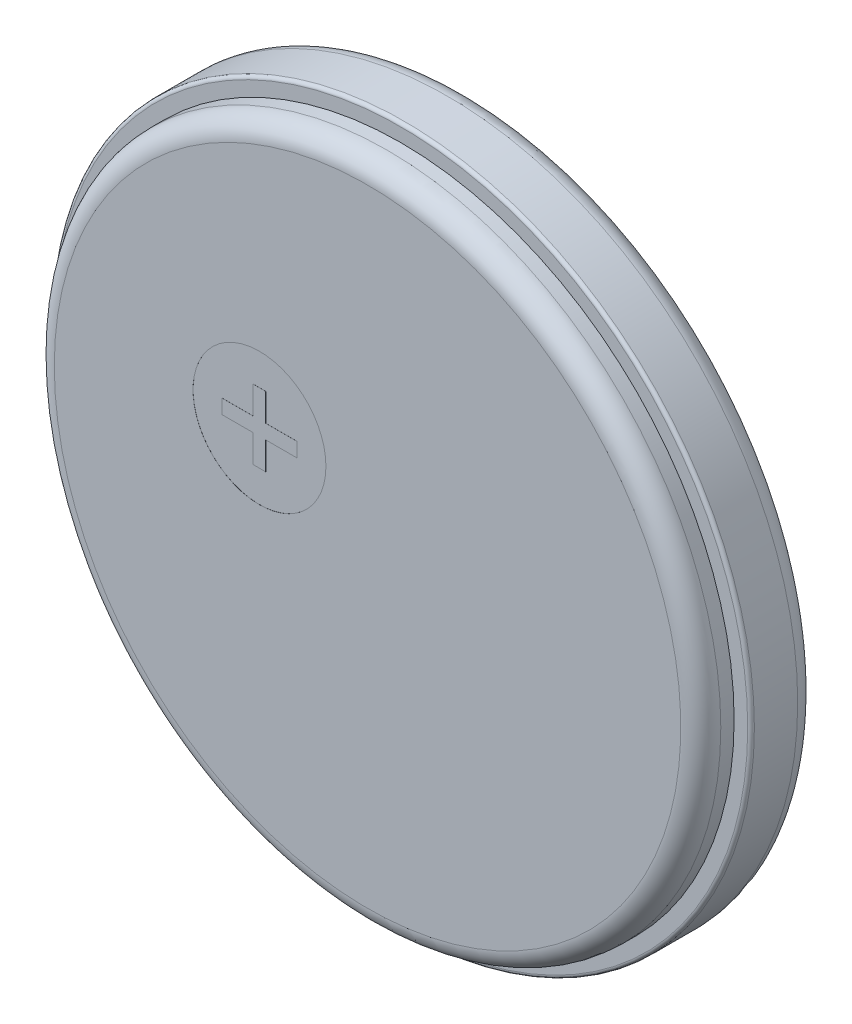
SolidWorks part; units mm, degrees
ref_plane "Front Plane" through (0, 0, 0) normal (0, 0, 1) x (1, 0, 0)
ref_plane "Top Plane" through (0, 0, 0) normal (0, 1, 0) x (1, 0, 0)
ref_plane "Right Plane" through (0, 0, 0) normal (1, 0, 0) x (0, 0, -1)
sketch "Sketch2" plane through (0, 0, 10.668) normal (0, 0, -1) x (-1, 0, 0)
  circle A0 centre (0, 31.75) radius 5
  dimension "D1" = 10
extrude "Boss-Extrude1" add sketch "Sketch2" along normal blind 0.5
fillet "Fillet1" radius 0.3 1 edges at (-5, 31.75, 10.668)
sketch "Sketch3" plane through (0, 0, 10.168) normal (0, 0, -1) x (-1, 0, 0)
  circle A2 centre (0, 31.75) radius 5.254
  circle A3 centre (0, 31.75) radius 5.254
  dimension "D1" = 0.254
extrude "Boss-Extrude2" add sketch "Sketch3" along normal blind 1
fillet "Fillet2" radius 0.3 1 edges at (-5.254, 31.75, 9.168)
fillet "Fillet3" radius 0.05 1 edges at (-5.254, 31.75, 10.168)
sketch "Sketch4" plane through (0, 0, 9.168) normal (0, 0, -1) x (-1, 0, 0)
  line L0 (-2.6501, 29.9289) -> (3.0044, 29.9289) construction
  line L1 (1.1417, 31.9299) -> (0.581, 33.5569)
  line L2 (0.581, 33.5569) -> (0.7228, 33.6419)
  line L3 (0.7228, 33.6419) -> (1.6489, 32.1001)
  line L4 (0.8246, 33.712) -> (1.7515, 32.1672)
  line L5 (0.8246, 33.712) -> (0.9402, 33.7813)
  line L6 (0.9402, 33.7813) -> (2.1566, 32.6492)
  arc A0 (1.6489, 32.1001) -> (1.7515, 32.1672) centre (0.992, 33.2168) ccw
  circle A1 centre (0.581, 33.947) radius 0.2042
  arc A3 (2.1566, 32.6492) -> (1.1417, 31.9299) centre (0.992, 33.2168) ccw
  text T0 "Lithium Ion" font "Impact" height in points 3
extrude "Cut-Extrude1" cut sketch "Sketch4" against normal blind 0.001
sketch "Sketch5" plane through (0, 0, 9.168) normal (0, 0, -1) x (-1, 0, 0)
  text T0 "Veltel" font "BankGothic Md BT" height in points 2
extrude "Cut-Extrude2" cut sketch "Sketch5" against normal blind 0.001
sketch "Sketch6" plane through (0, 0, 9.168) normal (0, 0, -1) x (-1, 0, 0)
  text T0 "CR5505" font "Century Gothic" height in points 2
extrude "Cut-Extrude3" cut sketch "Sketch6" against normal blind 0.001
sketch "Sketch7" plane through (0, 0, 9.168) normal (0, 0, -1) x (-1, 0, 0)
  line L1 (-1.3038, 33.2168) -> (-2.5226, 33.2168)
  line L2 (-1.3038, 33.2168) -> (-1.3038, 33.4152)
  line L3 (-1.3038, 33.4152) -> (-2.5226, 33.4152)
  line L4 (-2.5226, 33.2168) -> (-2.5226, 33.4152)
  line L5 (-1.3038, 33.2168) -> (-2.5226, 33.4152) construction
  line L6 (-1.3038, 33.4152) -> (-2.5226, 33.2168) construction
  circle A0 centre (-1.9132, 33.316) radius 0.8691
  point P0 (-1.9132, 33.316)
extrude "Cut-Extrude4" cut sketch "Sketch7" against normal blind 0.001
sketch "Sketch8" plane through (0, 0, 10.668) normal (0, 0, 1) x (1, 0, 0)
  line L0 (-1.7148, 32.5891) -> (-2.1834, 32.5891)
  line L1 (-1.7148, 31.9585) -> (-1.5276, 31.9585)
  line L2 (-1.7148, 32.5891) -> (-1.7148, 33.0042)
  line L3 (-1.7148, 33.0042) -> (-1.5276, 33.0042)
  line L4 (-1.5276, 31.9585) -> (-1.5276, 32.3736)
  line L5 (-1.7148, 31.9585) -> (-1.5276, 33.0042) construction
  line L6 (-1.7148, 33.0042) -> (-1.5276, 31.9585) construction
  line L7 (-1.059, 32.3736) -> (-1.5276, 32.3736)
  line L8 (-1.059, 32.3736) -> (-1.059, 32.5891)
  line L9 (-1.059, 32.5891) -> (-1.5276, 32.5891)
  line L10 (-2.1834, 32.3736) -> (-2.1834, 32.5891)
  line L11 (-1.059, 32.3736) -> (-2.1834, 32.5891) construction
  line L12 (-1.059, 32.5891) -> (-2.1834, 32.3736) construction
  line L13 (-1.7148, 31.9585) -> (-1.7148, 32.3736)
  line L14 (-1.5276, 32.5891) -> (-1.5276, 33.0042)
  line L16 (-1.7148, 32.3736) -> (-2.1834, 32.3736)
  circle A0 centre (-1.6212, 32.4814) radius 0.9969
  point P0 (-1.6212, 32.4814)
  point P5 (-1.6212, 32.4814)
extrude "Cut-Extrude5" cut sketch "Sketch8" against normal blind 0.001
